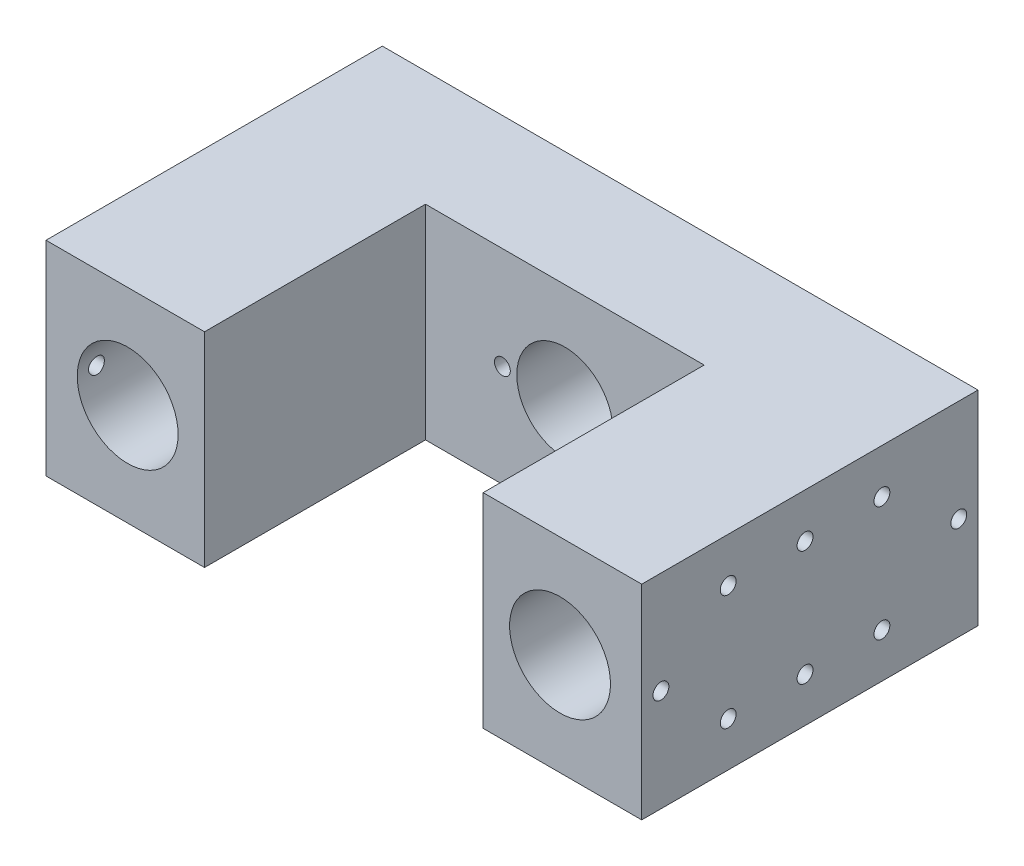
SolidWorks part; units mm, degrees
material "6061-O (SS)"
ref_plane "Front Plane" through (0, 0, 0) normal (0, 0, 1) x (1, 0, 0)
ref_plane "Top Plane" through (0, 0, 0) normal (0, 1, 0) x (1, 0, 0)
ref_plane "Right Plane" through (0, 0, 0) normal (1, 0, 0) x (0, 0, -1)
sketch "Sketch1" plane through (0, 0, 0) normal (0, 0, 1) x (1, 0, 0)
  line L0 (-17.1886, 21.25) -> (170.6689, 21.25) construction
  line L1 (0, 0) -> (124, 0)
  line L2 (0, 0) -> (0, 42.5)
  line L3 (0, 42.5) -> (124, 42.5)
  line L4 (124, 0) -> (124, 42.5)
  line L6 (62, 70.4734) -> (62, -38.8438) construction
  line L8 (17, 66.7901) -> (17, -52.1649) construction
  line L10 (107, -44.936) -> (107, 71.9278) construction
  circle A0 centre (17, 21.25) radius 10.5
  circle A1 centre (62, 21.25) radius 10
  circle A2 centre (107, 21.25) radius 10.5
  circle A3 centre (49, 21.25) radius 1.65
  circle A4 centre (75, 21.25) radius 1.65
  dimension "D5" = 21
  dimension "D6" = 26
  dimension "D7" = 3.3
  dimension "D8" = 20
  dimension "D1" = 124
  dimension "D2" = 42.5
  dimension "D3" = 17
  dimension "D4" = 17
extrude "Boss-Extrude1" add sketch "Sketch1" along normal blind 70
sketch "Sketch2" plane through (0, 0, 70) normal (0, 0, 1) x (1, 0, 0)
  line L0 (124, 42.5) -> (0, 42.5) construction
  line L1 (33, 42.5) -> (91, 42.5)
  line L2 (33, 42.5) -> (33, 0)
  line L3 (33, 0) -> (91, 0)
  line L4 (91, 42.5) -> (91, 0)
  line L5 (0, 0) -> (124, 0) construction
  line L6 (0, 42.5) -> (0, 0) construction
  line L7 (124, 0) -> (124, 42.5) construction
  dimension "D1" = 33
  dimension "D2" = 33
extrude "Cut-Extrude1" cut sketch "Sketch2" against normal offset from surface (46 mm away) 24 up to face at (50.65, 21.25, 0)
sketch "Sketch3" plane through (0, 0, 0) normal (0, 0, -1) x (-1, 0, 0)
  circle A0 centre (-62, 21.25) radius 18.35
  dimension "D1" = 36.7
extrude "Cut-Extrude2" cut sketch "Sketch3" against normal blind 5
sketch "Sketch5" plane through (124, 0, 0) normal (1, 0, 0) x (0, 0, -1)
  line L0 (-86.7923, 21.25) -> (13.7345, 21.25) construction
  line L1 (0, 0) -> (0, 42.5) construction
  line L2 (-70, 42.5) -> (0, 42.5) construction
  line L3 (-70, 0) -> (0, 0) construction
  line L4 (-70, 0) -> (-70, 42.5) construction
  circle A0 centre (-20, 9.25) radius 1.65
  circle A1 centre (-20, 33.25) radius 1.65
  circle A2 centre (-36, 33.25) radius 1.65
  circle A3 centre (-36, 9.25) radius 1.65
  circle A4 centre (-52, 9.25) radius 1.65
  circle A5 centre (-52, 33.25) radius 1.65
  circle A6 centre (-66, 21.25) radius 1.65
  circle A7 centre (-4, 21.25) radius 1.65
  circle A10 centre (-84, 33.25) radius 1.65 [skipped]
  circle A11 centre (-84, 9.25) radius 1.65 [skipped]
  circle A12 centre (-68, 9.25) radius 1.65 [skipped]
  circle A13 centre (-68, 33.25) radius 1.65 [skipped]
  circle A14 centre (-52, 33.25) radius 1.65 [skipped]
  circle A15 centre (-52, 9.25) radius 1.65 [skipped]
  dimension "D1" = 3.3
  dimension "D7" = 3.3
  dimension "D2" = 24
  dimension "D3" = 20
  dimension "D5" = 16
  dimension "D6" = 16
  dimension "D8" = 4
  dimension "D9" = 4
  dimension "D4" = 5
extrude "Cut-Extrude4" cut sketch "Sketch5" against normal blind 12
sketch "Sketch6" plane through (0, 0, 0) normal (-1, 0, 0) x (0, 0, 1)
  line L0 (-14.743, 21.25) -> (88.2582, 21.25) construction
  line L1 (0, 42.5) -> (0, 0) construction
  line L2 (70, 0) -> (0, 0) construction
  line L3 (70, 42.5) -> (0, 42.5) construction
  line L4 (70, 42.5) -> (70, 0) construction
  circle A0 centre (20, 33.25) radius 1.65
  circle A1 centre (36, 33.25) radius 1.65
  circle A2 centre (36, 9.25) radius 1.65
  circle A3 centre (20, 9.25) radius 1.65
  circle A4 centre (52, 33.25) radius 1.65
  circle A5 centre (52, 9.25) radius 1.65
  circle A6 centre (66, 21.25) radius 1.65
  circle A7 centre (4, 21.25) radius 1.65
  dimension "D4" = 3.3
  dimension "D6" = 3.3
  dimension "D1" = 24
  dimension "D2" = 20
  dimension "D3" = 16
  dimension "D5" = 16
  dimension "D7" = 4
  dimension "D8" = 4
extrude "Cut-Extrude5" cut sketch "Sketch6" against normal blind 12
sketch "Sketch4" plane through (0, 0, 0) normal (0, -1, 0) x (1, 0, 0)
  line L0 (17, 87.5581) -> (17, -28.945) construction
  line L1 (0, 70) -> (0, 0) construction
  line L2 (107, 91.6339) -> (107, -32.1205) construction
  line L4 (124, 70) -> (124, 0) construction
  line L5 (0, 70) -> (33, 70) construction
  line L6 (0, 0) -> (124, 0) construction
  line L7 (91, 70) -> (124, 70) construction
  circle A0 centre (17, 55) radius 2.1
  circle A1 centre (17, 15) radius 2.1
  circle A2 centre (107, 15) radius 2.1
  circle A3 centre (107, 55) radius 2.1
  dimension "D1" = 4.2
  dimension "D2" = 17
  dimension "D3" = 17
  dimension "D4" = 15
  dimension "D5" = 15
  dimension "D6" = 15
  dimension "D7" = 15
extrude "Cut-Extrude3" cut sketch "Sketch4" against normal up to next
